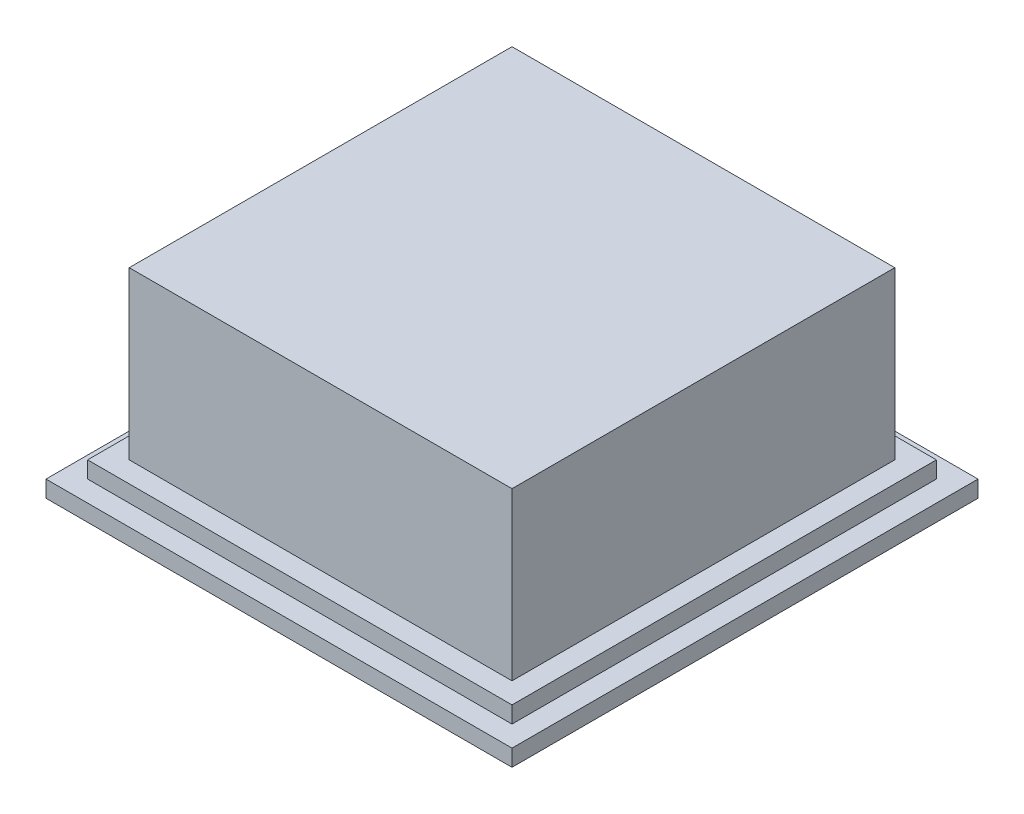
SolidWorks part; units mm, degrees
ref_plane "Front Plane" through (0, 0, 0) normal (0, 0, 1) x (1, 0, 0)
ref_plane "Top Plane" through (0, 0, 0) normal (0, 1, 0) x (1, 0, 0)
ref_plane "Right Plane" through (0, 0, 0) normal (1, 0, 0) x (0, 0, -1)
sketch "Sketch1" plane through (0, 0, 0) normal (0, 1, 0) x (1, 0, 0)
  line L1 (14, -14) -> (-14, -14)
  line L2 (14, -14) -> (14, 14)
  line L3 (14, 14) -> (-14, 14)
  line L4 (-14, -14) -> (-14, 14)
  line L5 (14, -14) -> (-14, 14) construction
  line L6 (14, 14) -> (-14, -14) construction
  point P0 (0, 0)
  dimension "D1" = 28
extrude "Boss-Extrude1" add sketch "Sketch1" along normal blind 1
sketch "Sketch2" plane through (0, 1, 0) normal (0, 1, 0) x (1, 0, 0)
  line L1 (12.75, -12.75) -> (-12.75, -12.75)
  line L2 (12.75, -12.75) -> (12.75, 12.75)
  line L3 (12.75, 12.75) -> (-12.75, 12.75)
  line L4 (-12.75, -12.75) -> (-12.75, 12.75)
  line L5 (12.75, -12.75) -> (-12.75, 12.75) construction
  line L6 (12.75, 12.75) -> (-12.75, -12.75) construction
  point P0 (0, 0)
  dimension "D1" = 25.5
extrude "Boss-Extrude2" add sketch "Sketch2" along normal blind 1
sketch "Sketch3" plane through (0, 2, 0) normal (0, 1, 0) x (1, 0, 0)
  line L1 (11.5, -11.5) -> (-11.5, -11.5)
  line L2 (11.5, -11.5) -> (11.5, 11.5)
  line L3 (11.5, 11.5) -> (-11.5, 11.5)
  line L4 (-11.5, -11.5) -> (-11.5, 11.5)
  line L5 (11.5, -11.5) -> (-11.5, 11.5) construction
  line L6 (11.5, 11.5) -> (-11.5, -11.5) construction
  point P0 (0, 0)
  dimension "D1" = 23
extrude "Boss-Extrude3" add sketch "Sketch3" along normal blind 10
